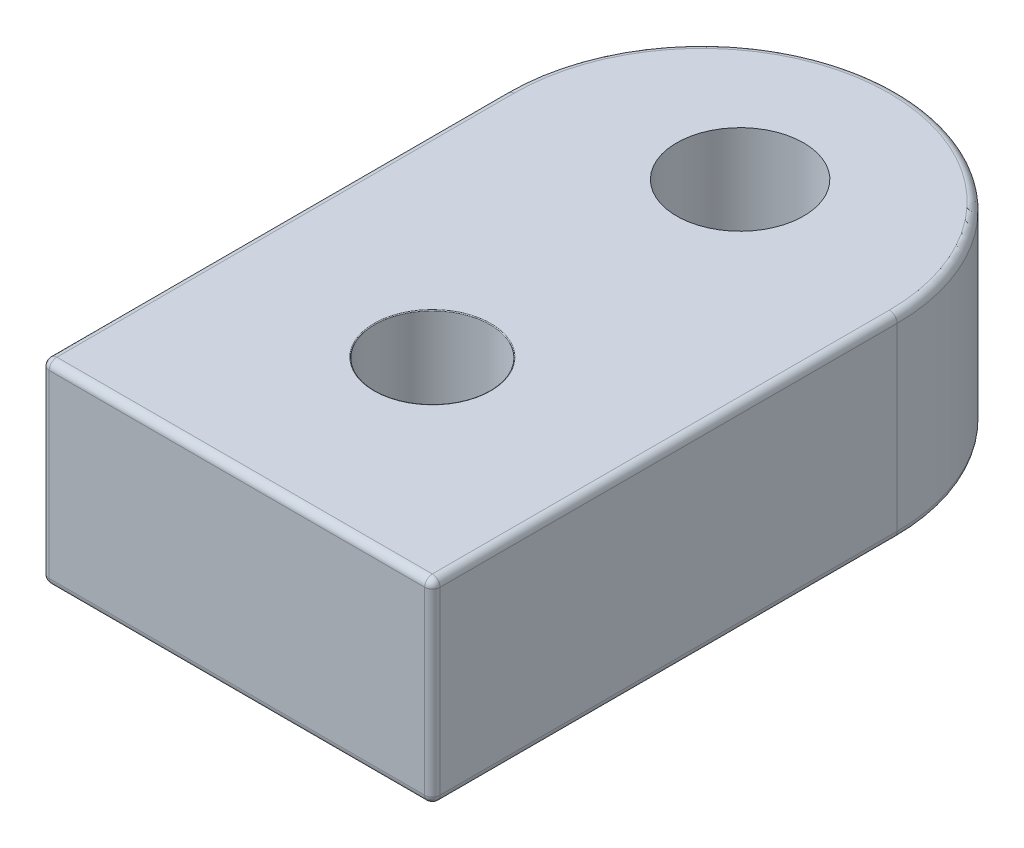
SolidWorks part; units mm, degrees
ref_plane "Front Plane" through (0, 0, 0) normal (0, 0, 1) x (1, 0, 0)
ref_plane "Top Plane" through (0, 0, 0) normal (0, 1, 0) x (1, 0, 0)
ref_plane "Right Plane" through (0, 0, 0) normal (1, 0, 0) x (0, 0, -1)
sketch "Sketch1" plane through (0, 0, 0) normal (0, 1, 0) x (1, 0, 0)
  line L1 (12.7, -17.5) -> (-12.7, -17.5)
  line L2 (12.7, -17.5) -> (12.7, 17.5)
  line L3 (12.7, 17.5) -> (-12.7, 17.5)
  line L4 (-12.7, -17.5) -> (-12.7, 17.5)
  line L5 (12.7, -17.5) -> (-12.7, 17.5) construction
  line L6 (12.7, 17.5) -> (-12.7, -17.5) construction
  point P0 (0, 0)
  dimension "D1" = 25.4
  dimension "D2" = 35
extrude "Boss-Extrude1" add sketch "Sketch1" along normal blind 12.7
sketch "Sketch2" plane through (0, 0, 0) normal (0, 0, 1) x (1, 0, 0)
  line L0 (0, 7.8396) -> (0, -1.854) construction
  line L2 (3.75, 12.7) -> (3.75, 4.5)
  line L3 (-12.7, 12.7) -> (12.7, 12.7) construction
  line L4 (3.75, 4.5) -> (2.05, 4.5)
  line L5 (2.05, 4.5) -> (2.05, 0)
  line L6 (55, 0) -> (-55, 0) construction
  line L7 (2.05, 0) -> (0, 0)
  line L8 (0, 0) -> (0, 12.7)
  line L9 (0, 12.7) -> (3.75, 12.7)
  dimension "D1" = 7.5
  dimension "D2" = 4.5
  dimension "D3" = 4.1
revolve "Cut-Revolve1" cut sketch "Sketch2" angle 360 about L0
fillet "Fillet1" radius 0.05 3 edges at (0, 4.5, 3.75) (0, 4.5, 2.05) (0, 12.7, 3.75)
sketch "Sketch4" plane through (0, 0, 0) normal (0, -1, 0) x (1, 0, 0)
  line L0 (0, -55) -> (0, 55) construction
  line L1 (-13.2725, 0) -> (22.9365, 0) construction
  circle A0 centre (0, 10.16) radius 0.775
  circle A1 centre (0, -10.16) radius 0.775
  dimension "D1" = 1.55
  dimension "D2" = 20.32
extrude "Boss-Extrude2" add sketch "Sketch4" along normal blind 2
fillet "Fillet2" radius 0.1 2 edges at (0, -2, -9.385) (0, -2, 9.385)
sketch "Sketch9" plane through (0, 12.7, 0) normal (0, 1, 0) x (1, 0, 0)
  line L0 (12.7, 17.5) -> (-12.7, 17.5) construction
  line L1 (0, -55) -> (0, 55) construction
  line L2 (12.7, 17.5) -> (-12.7, 17.5)
  arc A0 (12.7, 17.5) -> (-12.7, 17.5) centre (0, 17.5) ccw
extrude "Boss-Extrude3" add sketch "Sketch9" against normal up to surface (12.7 mm away) up to face at (0, 0, -9.385)
fillet "Fillet3" radius 0.5 7 edges at (12.7, 0, 0) (0, 0, -30.2) (0, 12.7, -30.2) (-12.7, 0, 0) (0, 0, 17.5) (12.7, 12.7, 0) (-12.7, 12.7, 0)
sketch "Sketch12" plane through (0, 0, 0) normal (0, 1, 0) x (1, 0, 0)
  line L0 (-12.7, -17.5) -> (12.7, -17.5) construction
  line L1 (15.5008, -12.7) -> (-13.4525, -12.7)
  line L2 (15.5008, -12.7) -> (15.5008, -17.5)
  line L3 (15.5008, -17.5) -> (-13.4525, -17.5)
  line L4 (-13.4525, -12.7) -> (-13.4525, -17.5)
  dimension "D1" = 4.8
extrude "Cut-Extrude6" cut sketch "Sketch12" against normal through all and the other way through all
sketch "Sketch10" plane through (0, 0, 0) normal (0, -1, 0) x (1, 0, 0)
  circle A0 centre (0, -20) radius 4.125
  dimension "D1" = 8.25
  dimension "D2" = 20
extrude "Cut-Extrude1" cut sketch "Sketch10" against normal through all both and the other way through all
sketch "Sketch11" plane through (0, 0, 0) normal (0, -1, 0) x (1, 0, 0)
  circle A0 centre (0, -10.16) radius 0.9
  circle A1 centre (0, 10.16) radius 0.9
  dimension "D1" = 1.8
extrude "Cut-Extrude3" cut sketch "Sketch11" against normal blind 5 and the other way through all
fillet "Fillet4" radius 0.5 8 edges at (0, 12.7, 12.7) (12.5536, 12.5536, 12.7) (12.7, 6.35, 12.7) (12.5536, 0.1464, 12.7) (0, 0, 12.7) (-12.5536, 0.1464, 12.7) (-12.7, 6.35, 12.7) (-12.5536, 12.5536, 12.7)
